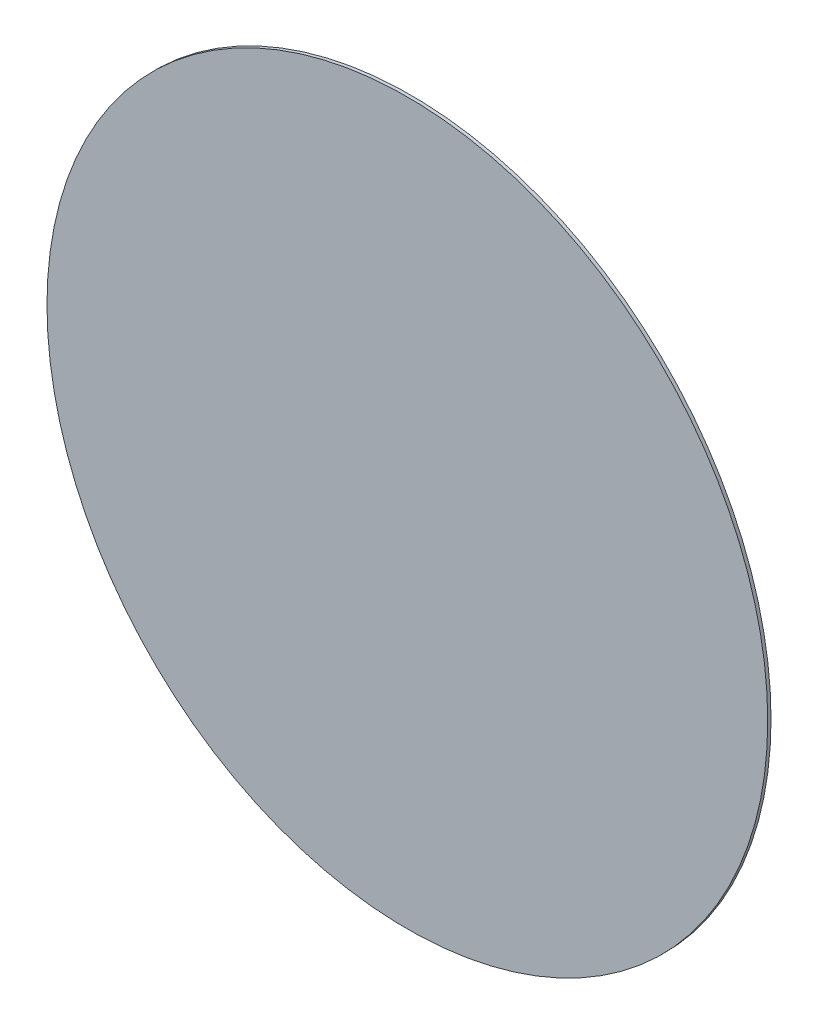
SolidWorks part; units mm, degrees
ref_plane "前视基准面" through (0, 0, 0) normal (0, 0, 1) x (1, 0, 0)
ref_plane "上视基准面" through (0, 0, 0) normal (0, 1, 0) x (1, 0, 0)
ref_plane "右视基准面" through (0, 0, 0) normal (1, 0, 0) x (0, 0, -1)
other "Configuration Table"
sketch "草图1" plane through (0, 0, 0) normal (0, 0, 1) x (1, 0, 0)
  circle A0 centre (0, 0) radius 11
  dimension "D1" = 22
extrude "凸台-拉伸1" add sketch "草图1" along normal blind 0.1
